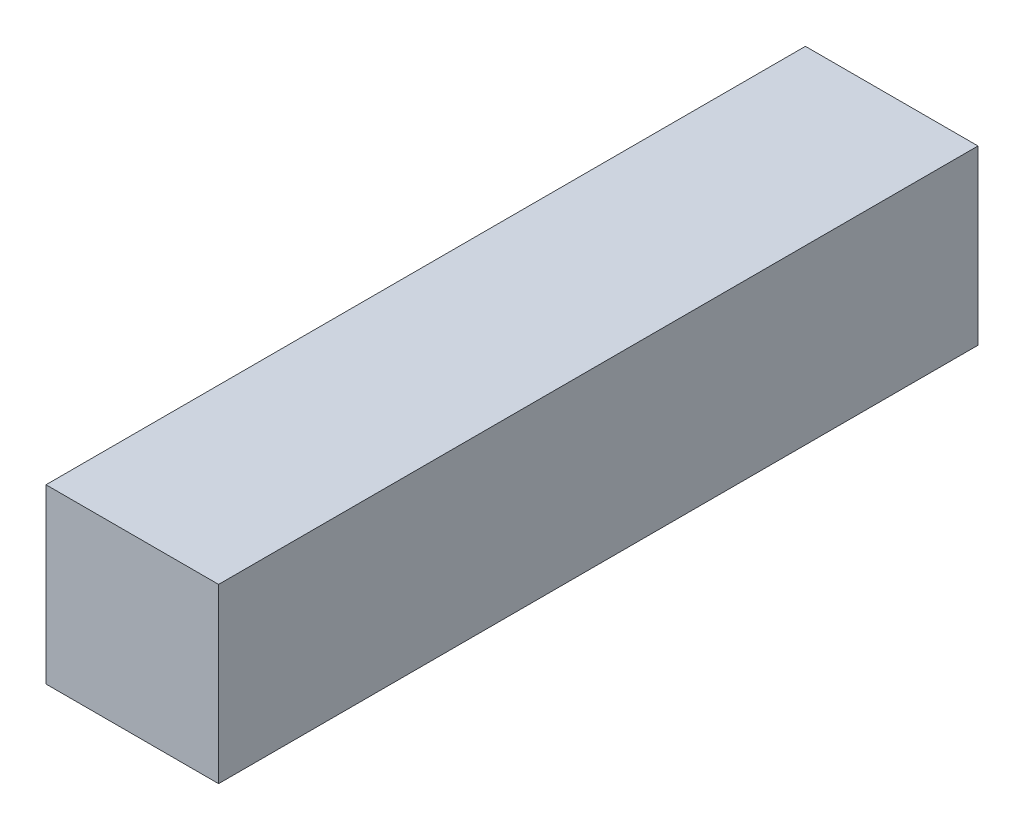
SolidWorks part; units mm, degrees
ref_plane "Front Plane" through (0, 0, 0) normal (0, 0, 1) x (1, 0, 0)
ref_plane "Top Plane" through (0, 0, 0) normal (0, 1, 0) x (1, 0, 0)
ref_plane "Right Plane" through (0, 0, 0) normal (1, 0, 0) x (0, 0, -1)
sketch "Sketch1" plane through (0, 0, 0) normal (0, 0, 1) x (1, 0, 0)
  line L0 (0, 0) -> (0, -12.5)
  line L1 (0, -12.5) -> (12.5, -12.5)
  line L2 (12.5, -12.5) -> (12.5, 0)
  line L3 (12.5, 0) -> (0, 0)
  dimension "D1" = 12.5
  dimension "D2" = 12.5
extrude "Boss-Extrude1" add sketch "Sketch1" along normal blind 55
